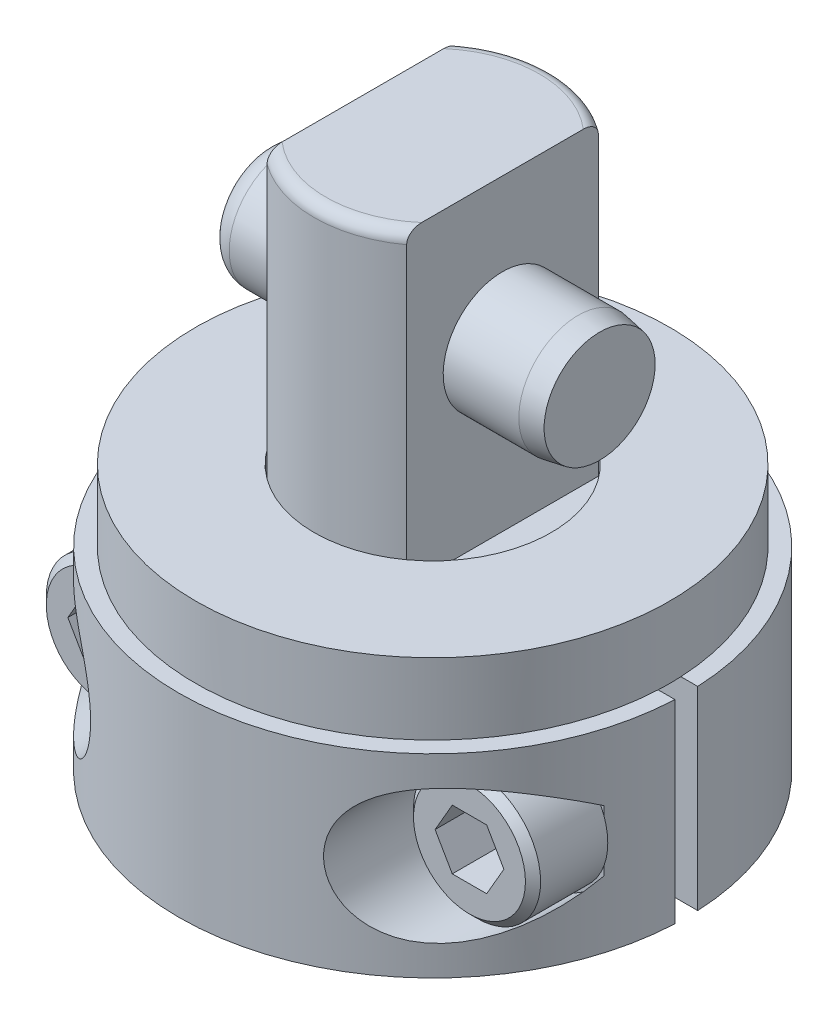
SolidWorks part; units mm, degrees
material "Alloy Steel"
ref_plane "Front Plane" through (0, 0, 0) normal (0, 0, 1) x (1, 0, 0)
ref_plane "Top Plane" through (0, 0, 0) normal (0, 1, 0) x (1, 0, 0)
ref_plane "Right Plane" through (0, 0, 0) normal (1, 0, 0) x (0, 0, -1)
sketch "Sketch1" plane through (0, 0, 0) normal (1, 0, 0) x (0, 0, -1)
  line L0 (0, 30.3276) -> (7.9375, 30.3276)
  line L1 (7.9375, 30.3276) -> (7.9375, 1.3462)
  line L2 (7.9375, 1.3462) -> (5.0038, 1.3462)
  line L3 (5.0038, 1.3462) -> (5.0038, -9.8298)
  line L4 (5.0038, -9.8298) -> (0, -9.8298)
  line L5 (0, -9.8298) -> (0, 30.3276)
  line L6 (0, -15.3594) -> (0, 43.147) construction
  dimension "D1" = 40.1574
  dimension "D2" = 11.176
  dimension "D3" = 10.0076
  dimension "D4" = 15.875
  dimension "D5" = 1.3462
revolve "Revolve1" add sketch "Sketch1" angle 360 about L6
fillet "Fillet1" radius 0.7874 1 edges at (0, 30.3276, -7.9375)
sketch "Sketch2" plane through (0, 0, 0) normal (0, 0, 1) x (1, 0, 0)
  line L0 (4.6736, 30.3276) -> (7.9375, 30.3276)
  line L1 (7.9375, 30.3276) -> (7.9375, 9.7028)
  line L2 (7.9375, 9.7028) -> (4.6736, 9.7028)
  line L3 (4.6736, 9.7028) -> (4.6736, 30.3276)
  line L4 (-7.9375, 30.3276) -> (-4.6736, 30.3276)
  line L5 (-4.6736, 30.3276) -> (-4.6736, 9.7028)
  line L6 (-4.6736, 9.7028) -> (-7.9375, 9.7028)
  line L7 (-7.9375, 9.7028) -> (-7.9375, 30.3276)
  line L8 (0, 5.9766) -> (0, 42.131) construction
  line L9 (7.1501, 30.3276) -> (-7.1501, 30.3276) construction
  line L10 (7.9375, 1.3462) -> (7.9375, 29.5402) construction
  line L11 (-7.9375, 29.5402) -> (-7.9375, 1.3462) construction
  dimension "D1" = 9.3472
  dimension "D2" = 20.6248
extrude "Cut-Extrude1" cut sketch "Sketch2" against normal through all and the other way through all
sketch "Sketch3" plane through (0, 1.3462, 0) normal (0, -1, 0) x (1, 0, 0)
  circle A0 centre (0, 0) radius 3.9624
  circle A1 centre (0, 0) radius 5.0038 construction
  circle A2 centre (0, 0) radius 5.0038
  dimension "D1" = 7.9248
extrude "Cut-Extrude2" cut sketch "Sketch3" along normal blind 2.54
chamfer "Chamfer1" distance 0.762 angle 45 1 edges at (0, -9.8298, -5.0038)
sketch "Sketch4" plane through (0, 0, 0) normal (1, 0, 0) x (0, 0, -1)
  line L0 (-7.9375, 1.3462) -> (7.9375, 1.3462) construction
  circle A0 centre (0, 20.8026) radius 3.9713
  dimension "D1" = 7.9426
  dimension "D2" = 19.4564
extrude "Extrude1" add sketch "Sketch4" along normal mid plane 22.352
chamfer "Chamfer2" distance 0.254 angle 80 1 edges at (11.176, 20.8026, -3.9713)
fillet "Fillet2" radius 1.524 1 edges at (-11.176, 20.8026, -3.9713)
sketch "Sketch5" plane through (0, 0, 0) normal (0, 1, 0) x (1, 0, 0)
  line L0 (7.9008, 0.762) -> (16.9829, 0.762)
  line L1 (7.9008, -0.762) -> (16.9829, -0.762)
  line L2 (-7.9008, -0.762) -> (-16.9829, -0.762)
  line L3 (-7.9008, 0.762) -> (-16.9829, 0.762)
  line L4 (0, 0) -> (24.3028, 0) construction
  arc A0 (16.9829, 0.762) -> (-16.9829, 0.762) centre (0, 0) ccw
  arc A1 (-16.9829, -0.762) -> (16.9829, -0.762) centre (0, 0) ccw
  arc A2 (7.9008, 0.762) -> (-7.9008, 0.762) centre (0, 0) ccw
  arc A3 (-7.9008, -0.762) -> (7.9008, -0.762) centre (0, 0) ccw
  circle A4 centre (0, 0) radius 7.9375 construction
  dimension "D2" = 17
  dimension "D1" = 1.524
extrude "Extrude2" add sketch "Sketch5" along normal blind 6.5 and the other way blind 6.5
sketch "Sketch6" plane through (0, 0, 0.762) normal (0, 0, 1) x (1, 0, 0)
  line L0 (0, -5.6718) -> (0, 5.6718) construction
  line L1 (-16.9829, -6.5) -> (16.9829, -6.5) construction
  circle A0 centre (12.2936, 0) radius 4.4958
  circle A1 centre (-12.2936, 0) radius 4.4958
  dimension "D1" = 8.9916
  dimension "D2" = 24.5872
  dimension "D3" = 6.5
extrude "Cut-Extrude3" cut sketch "Sketch6" along normal through all from offset 4.064
sketch "Sketch7" plane through (0, 0, 4.826) normal (0, 0, 1) x (1, 0, 0)
  circle A0 centre (12.2936, 0) radius 4.2545
  circle A1 centre (-12.2936, 0) radius 4.2545
  arc A3 (-16.3006, -2.0387) -> (-16.3006, 2.0387) centre (-12.2936, 0) ccw construction
  arc A4 (16.3006, 2.0387) -> (16.3006, -2.0387) centre (12.2936, 0) ccw construction
  dimension "D1" = 8.509
extrude "Extrude3" add sketch "Sketch7" along normal blind 5.0038
chamfer "Chamfer3" distance 0.508 angle 45 2 edges at (-8.0391, 0, 9.8298) (16.5481, 0, 9.8298)
sketch "Sketch8" plane through (0, 0, 9.8298) normal (0, 0, 1) x (1, 0, 0)
  line L0 (0, 0) -> (0, -21.769) construction
  line L1 (13.4448, 1.9939) -> (14.596, 0)
  line L2 (11.1424, 1.9939) -> (13.4448, 1.9939)
  line L3 (9.9912, 0) -> (11.1424, 1.9939)
  line L4 (11.1424, -1.9939) -> (9.9912, 0)
  line L5 (13.4448, -1.9939) -> (11.1424, -1.9939)
  line L6 (14.596, 0) -> (13.4448, -1.9939)
  line L8 (-14.596, 0) -> (-13.4448, -1.9939)
  line L9 (-13.4448, -1.9939) -> (-11.1424, -1.9939)
  line L10 (-11.1424, -1.9939) -> (-9.9912, 0)
  line L11 (-9.9912, 0) -> (-11.1424, 1.9939)
  line L12 (-11.1424, 1.9939) -> (-13.4448, 1.9939)
  line L13 (-13.4448, 1.9939) -> (-14.596, 0)
  circle A0 centre (-12.2936, 0) radius 1.9939 construction
  circle A1 centre (12.2936, 0) radius 1.9939 construction
  dimension "D2" = 3.9878
extrude "Cut-Extrude4" cut sketch "Sketch8" against normal blind 3.9878
sketch "Sketch10" plane through (0, 0, 0) normal (0, 0, 1) x (1, 0, 0)
  circle A0 centre (12.2936, 0) radius 2.5019
  circle A1 centre (-12.2936, 0) radius 2.5019
  circle A2 centre (-12.2936, 0) radius 4.2545 construction
  circle A3 centre (12.2936, 0) radius 4.2545 construction
  dimension "D1" = 5.0038
extrude "Extrude4" add sketch "Sketch10" along normal up to next and the other way up to next
sketch "Sketch11" plane through (0, 6.5, 0) normal (0, 1, 0) x (-1, 0, 0)
  circle A0 centre (0, 0) radius 15.875
  circle A1 centre (0, 0) radius 7.9375
  circle A3 centre (0, 0) radius 5.0038 construction
  dimension "D1" = 31.75
  dimension "D2" = 15.875
extrude "Extrude5" add sketch "Sketch11" along normal blind 4.7749
